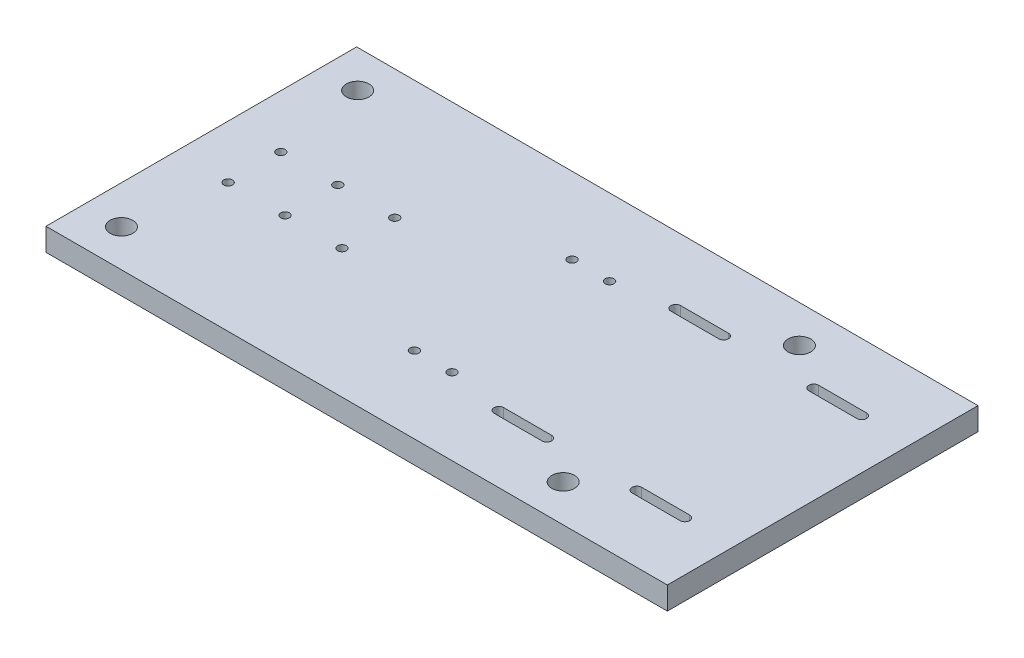
SolidWorks part; units mm, degrees
ref_plane "Front Plane" through (0, 0, 0) normal (0, 0, 1) x (1, 0, 0)
ref_plane "Top Plane" through (0, 0, 0) normal (0, 1, 0) x (1, 0, 0)
ref_plane "Right Plane" through (0, 0, 0) normal (1, 0, 0) x (0, 0, -1)
sketch "Sketch1" plane through (0, 0, 0) normal (0, 1, 0) x (1, 0, 0)
  line L1 (0, 0) -> (304.8, 0)
  line L2 (0, 0) -> (0, 152.4)
  line L3 (0, 152.4) -> (304.8, 152.4)
  line L4 (304.8, 0) -> (304.8, 152.4)
  dimension "D1" = 152.4
  dimension "D2" = 304.8
extrude "Boss-Extrude1" add sketch "Sketch1" along normal blind 11.1125
sketch "Sketch2" plane through (0, 11.1125, 0) normal (0, 1, 0) x (1, 0, 0)
  line L0 (165.1, 43.8952) -> (165.1, 31.1952)
  line L1 (165.1, 31.1952) -> (139.7, 31.1952)
  line L2 (139.7, 31.1952) -> (139.7, 43.8952)
  line L3 (139.7, 43.8952) -> (165.1, 43.8952)
  line L4 (139.7, 108.5048) -> (165.1, 108.5048)
  line L5 (165.1, 108.5048) -> (165.1, 121.2048)
  line L6 (165.1, 121.2048) -> (139.7, 121.2048)
  line L7 (139.7, 121.2048) -> (139.7, 108.5048)
  dimension "D1" = 25.4
  dimension "D2" = 12.7
sketch "Sketch3" plane through (0, 11.1125, 0) normal (0, 1, 0) x (1, 0, 0)
  line L0 (201.0961, 40.64) -> (201.0961, 111.76) construction
  line L1 (191.5711, 40.64) -> (210.6211, 40.64) construction
  line L2 (210.6211, 111.76) -> (191.5711, 111.76) construction
  line L3 (268.8039, 40.64) -> (268.8039, 111.76) construction
  line L4 (259.2789, 40.64) -> (278.3289, 40.64) construction
  line L5 (278.3289, 111.76) -> (259.2789, 111.76) construction
  line L8 (304.8, 76.2) -> (165.1, 76.2) construction
  line L9 (268.8039, 40.64) -> (268.8039, 32.8229) construction
  line L10 (280.5677, 32.8229) -> (257.04, 32.8229) construction
  line L11 (257.04, 30.4416) -> (280.5677, 30.4416)
  line L12 (257.04, 35.2041) -> (280.5677, 35.2041)
  line L13 (304.8, 0) -> (304.8, 152.4) construction
  line L14 (165.1, 114.3) -> (165.1, 38.1) construction
  line L15 (234.95, 76.2) -> (234.95, 0) construction
  line L16 (0, 0) -> (304.8, 0) construction
  line L17 (280.5677, 119.5771) -> (257.04, 119.5771) construction
  line L18 (257.04, 117.1959) -> (280.5677, 117.1959)
  line L19 (257.04, 121.9584) -> (280.5677, 121.9584)
  line L20 (189.3323, 32.8229) -> (212.86, 32.8229) construction
  line L21 (189.3323, 119.5771) -> (212.86, 119.5771) construction
  line L22 (212.86, 121.9584) -> (189.3323, 121.9584)
  line L23 (212.86, 117.1959) -> (189.3323, 117.1959)
  line L24 (212.86, 35.2041) -> (189.3323, 35.2041)
  line L25 (212.86, 30.4416) -> (189.3323, 30.4416)
  circle A0 centre (257.04, 32.8229) radius 2.3813
  circle A1 centre (280.5677, 32.8229) radius 2.3813
  circle A2 centre (280.5677, 119.5771) radius 2.3813
  circle A3 centre (257.04, 119.5771) radius 2.3813
  circle A4 centre (189.3323, 32.8229) radius 2.3813
  circle A5 centre (189.3323, 119.5771) radius 2.3813
  circle A6 centre (212.86, 119.5771) radius 2.3813
  circle A7 centre (212.86, 32.8229) radius 2.3813
  point P19 (268.8039, 32.8229)
  dimension "D1" = 4.7625
extrude "Cut-Extrude2" cut sketch "Sketch3" against normal blind 11.1125 contours A1 L12 A0 L11 | L11 A1 L12 | A0 | L25 A7 L24 A4 | A6 L22 A5 L23 | L19 A3 L18 A2 | A2 L18 L19 | A3 | L23 A5 L22 | A6 | A7 | A4 L25 L24
ref_plane "Plane1" through (0, 0, -76.2) normal (0, 0, 1) x (1, 0, 0)
sketch "Sketch10" plane through (0, 0, 0) normal (0, -1, 0) x (1, 0, 0)
  line L0 (235.4487, -152.4) -> (235.4487, 0) construction
  line L1 (304.8, -152.4) -> (0, -152.4) construction
  line L2 (0, 0) -> (304.8, 0) construction
  line L3 (37.4991, -76.2) -> (0, -76.2) construction
  line L4 (6.1119, -76.2) -> (-6.1119, -76.2) construction
  line L5 (18.7496, -152.4) -> (18.7496, 0) construction
  line L6 (18.7496, -18.2506) -> (18.7496, -134.1494)
  line L7 (235.4487, -134.1494) -> (235.4487, -18.2506)
  circle A0 centre (18.7496, -134.1494) radius 5.5562
  circle A1 centre (18.7496, -18.2506) radius 5.5563
  circle A2 centre (235.4487, -134.1494) radius 5.5563
  circle A3 centre (235.4487, -18.2506) radius 5.5563
  point P20 (18.7496, -76.2)
  point P21 (235.4487, -76.2)
  dimension "D1" = 11.1125
extrude "Cut-Extrude9" cut sketch "Sketch10" against normal through all
sketch "Sketch12" plane through (0, 0, 0) normal (0, -1, 0) x (1, 0, 0)
  line L0 (152.6465, -43.8952) -> (152.6465, -108.5048) construction
  line L1 (152.6465, -76.2) -> (109.8819, -76.2) construction
  line L2 (109.8819, -152.4) -> (109.8819, 0) construction
  line L3 (109.8819, -76.2) -> (0, -76.2) construction
  line L4 (81.9419, -152.4) -> (81.9419, 0) construction
  line L5 (54.0019, -152.4) -> (54.0019, 0) construction
  line L6 (26.0619, -152.4) -> (26.0619, 0) construction
  line L7 (109.8819, -76.2) -> (81.9419, -76.2) construction
  line L8 (81.9419, -76.2) -> (54.0019, -76.2) construction
  line L9 (54.0019, -76.2) -> (26.0619, -76.2) construction
  line L10 (26.0619, -89.1336) -> (26.0619, -63.2664)
  line L11 (54.0019, -63.2664) -> (54.0019, -89.1336)
  line L12 (81.9419, -63.2664) -> (81.9419, -89.1336)
  circle A0 centre (81.9419, -63.2664) radius 4.1148
  circle A1 centre (54.0019, -63.2664) radius 4.1148
  circle A2 centre (26.0619, -63.2664) radius 4.1148
  circle A3 centre (26.0619, -89.1336) radius 4.1148
  circle A4 centre (54.0019, -89.1336) radius 4.1148
  circle A5 centre (81.9419, -89.1336) radius 4.1148
  point P7 (109.8819, -76.2)
  point P11 (81.9419, -76.2)
  point P14 (54.0019, -76.2)
  point P17 (26.0619, -76.2)
  point P32 (81.9419, -76.2)
  point P33 (26.0619, -76.2)
  point P34 (54.0019, -76.2)
  dimension "D1" = 27.94
sketch "Sketch14" plane through (0, 0, 0) normal (0, -1, 0) x (1, 0, 0)
  line L0 (139.7, -114.8548) -> (165.1, -114.8548) construction
  line L9 (139.7, -31.1952) -> (165.1, -31.1952) construction
  line L10 (139.7, -31.1952) -> (139.7, -43.8952) construction
  line L11 (139.7, -43.8952) -> (165.1, -43.8952) construction
  line L12 (165.1, -31.1952) -> (165.1, -43.8952) construction
  line L13 (165.1, -108.5048) -> (139.7, -108.5048) construction
  line L14 (165.1, -108.5048) -> (165.1, -121.2048) construction
  line L15 (165.1, -121.2048) -> (139.7, -121.2048) construction
  line L16 (139.7, -108.5048) -> (139.7, -121.2048) construction
  line L17 (165.1, -37.5452) -> (139.7, -37.5452) construction
  line L18 (143.1925, -37.5452) -> (143.1925, -43.8952) construction
  line L19 (143.1925, -43.8952) -> (143.1925, -37.5452) construction
  line L20 (161.6075, -37.5452) -> (161.6075, -43.8952) construction
  line L21 (161.6075, -43.8952) -> (161.6075, -37.5452) construction
  line L22 (143.1925, -114.8548) -> (143.1925, -108.5048) construction
  line L23 (161.6075, -114.8548) -> (161.6075, -108.5048) construction
  line L24 (161.6075, -108.5048) -> (161.6075, -114.8548) construction
hole_wizard "CBORE for #8 Socket Head Cap Screw1" positions "3DSketch1" profile "Sketch16" counterbore size "#8" standard "ANSI Inch" end condition up to next
sketch3d "3DSketch1"
  point P0 (143.1925, 0, -37.5452)
  point P3 (161.6075, 0, -37.5452)
  point P6 (161.6075, 0, -114.8548)
  point P9 (143.1925, 0, -114.8548)
sketch "Sketch16" plane through (143.1925, 0, -37.5452) normal (1, 0, 0) x (0, 0, -1)
  line L0 (0, 0) -> (0, 11.1125)
  line L1 (0, 11.1125) -> (2.1526, 11.1125)
  line L3 (2.1526, 11.1125) -> (2.1527, 4.1656)
  line L4 (2.1527, 4.1656) -> (3.9688, 4.1656)
  line L5 (3.9688, 4.1656) -> (3.9688, 0)
  line L7 (3.9688, 0) -> (0, 0)
  line L11 (0, -6.35) -> (0, 107.95) construction
  dimension "Thru Hole Dia." = 4.3053
  dimension "Thru Hole Depth" = 11.1125
  dimension "C'Bore Dia." = 7.9375
  dimension "C'Bore Depth" = 4.1656
hole_wizard "CBORE for #8 Socket Head Cap Screw2" positions "3DSketch2" profile "Sketch17" counterbore size "#8" standard "ANSI Inch" end condition up to next
sketch3d "3DSketch2"
  point P0 (26.0619, 0, -89.1336)
  point P3 (26.0619, 0, -63.2664)
  point P6 (54.0019, 0, -63.2664)
  point P9 (54.0019, 0, -89.1336)
  point P12 (81.9419, 0, -89.1336)
  point P15 (81.9419, 0, -63.2664)
sketch "Sketch17" plane through (26.0619, 0, -89.1336) normal (1, 0, 0) x (0, 0, -1)
  line L0 (0, 0) -> (0, 11.1125)
  line L1 (0, 11.1125) -> (2.1526, 11.1125)
  line L3 (2.1526, 11.1125) -> (2.1526, 4.1656)
  line L4 (2.1526, 4.1656) -> (3.9688, 4.1656)
  line L5 (3.9688, 4.1656) -> (3.9688, 0)
  line L7 (3.9688, 0) -> (0, 0)
  line L11 (0, -6.35) -> (0, 107.95) construction
  dimension "Thru Hole Dia." = 4.3053
  dimension "Thru Hole Depth" = 11.1125
  dimension "C'Bore Dia." = 7.9375
  dimension "C'Bore Depth" = 4.1656
sketch "Sketch22" plane through (0, 0, -35.2041) normal (0, 0, 1) x (1, 0, 0)
  line L0 (189.3323, 0) -> (212.86, 0)
  line L1 (212.86, 0) -> (212.86, 2.54)
  line L2 (212.86, 2.54) -> (189.3323, 2.54)
  line L3 (189.3323, 2.54) -> (189.3323, 0)
  line L4 (257.04, 0) -> (280.4766, 0)
  line L5 (0, 0) -> (304.8, 0) construction
  line L6 (280.4766, 0) -> (280.4766, 2.54)
  line L7 (280.4766, 2.54) -> (257.04, 2.54)
  line L8 (257.04, 2.54) -> (257.04, 0)
  dimension "D1" = 2.54
  dimension "D2" = 2.54
extrude "Cut-Extrude10" cut sketch "Sketch22" against normal up to next
